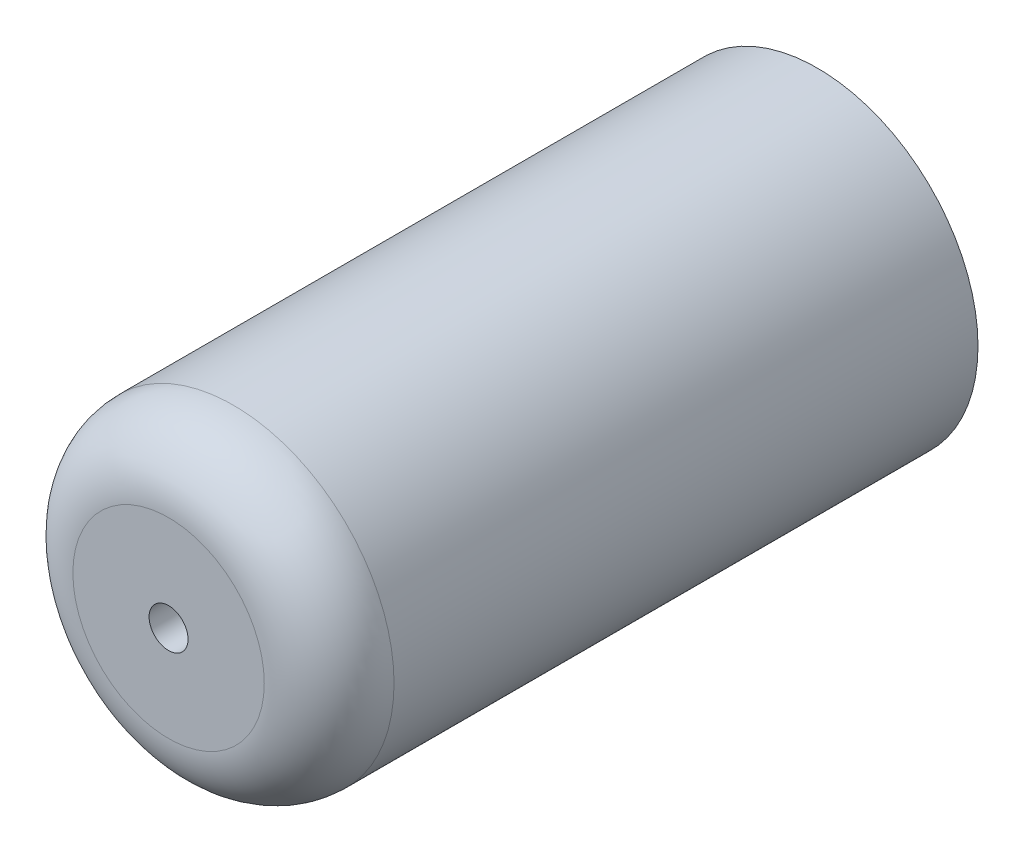
SolidWorks part; units mm, degrees
material "Plastique personnalisé"
ref_plane "Plan de face" through (0, 0, 0) normal (0, 0, 1) x (1, 0, 0)
ref_plane "Plan de dessus" through (0, 0, 0) normal (0, 1, 0) x (1, 0, 0)
ref_plane "Plan de droite" through (0, 0, 0) normal (1, 0, 0) x (0, 0, -1)
sketch "Esquisse1" plane through (0, 0, 0) normal (0, 0, 1) x (1, 0, 0)
  circle A0 centre (0, 0) radius 12.375
  dimension "D2" = 24.75
extrude "Boss.-Extru.1" add sketch "Esquisse1" along normal blind 50
fillet "Congé2" radius 5 1 edges at (12.375, 0, 50)
sketch "Esquisse2" plane through (0, 0, 0) normal (0, 0, -1) x (-1, 0, 0)
  circle A0 centre (0, 0) radius 1.5
extrude "Enlèv. mat.-Extru.1" cut sketch "Esquisse2" against normal through all
ref_plane "planespaceur" through (0, 0, 0) normal (1, 0, 0) x (0, 0, -1)
